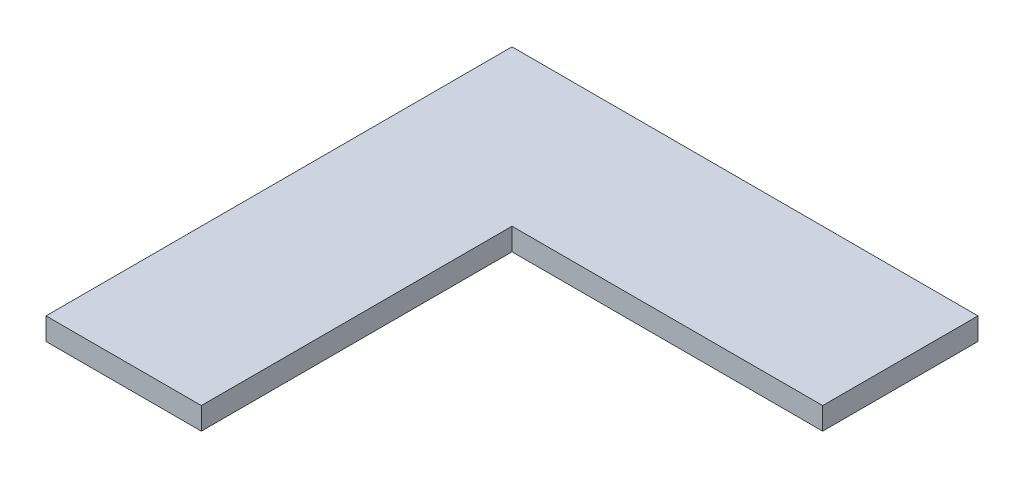
SolidWorks part; units mm, degrees
ref_plane "Front Plane" through (0, 0, 0) normal (0, 0, 1) x (1, 0, 0)
ref_plane "Top Plane" through (0, 0, 0) normal (0, 1, 0) x (1, 0, 0)
ref_plane "Right Plane" through (0, 0, 0) normal (1, 0, 0) x (0, 0, -1)
sketch "Sketch1" plane through (0, 0, 0) normal (0, 1, 0) x (1, 0, 0)
  line L0 (-105, 105) -> (105, -105) construction
  line L1 (-105, 105) -> (105, 105) construction
  line L2 (-105, 105) -> (-105, -105) construction
  line L3 (-105, -105) -> (105, -105) construction
  line L4 (105, 105) -> (105, -105) construction
  line L5 (-105, -105) -> (-105, 105)
  line L6 (-105, 105) -> (105, 105)
  line L7 (105, 105) -> (105, 35)
  line L8 (105, 35) -> (-35, 35)
  line L9 (-35, 35) -> (-35, -105)
  line L10 (-35, -105) -> (-105, -105)
  dimension "D1" = 210
  dimension "D2" = 210
  dimension "D3" = 70
  dimension "D4" = 70
extrude "Boss-Extrude1" add sketch "Sketch1" along normal blind 10
